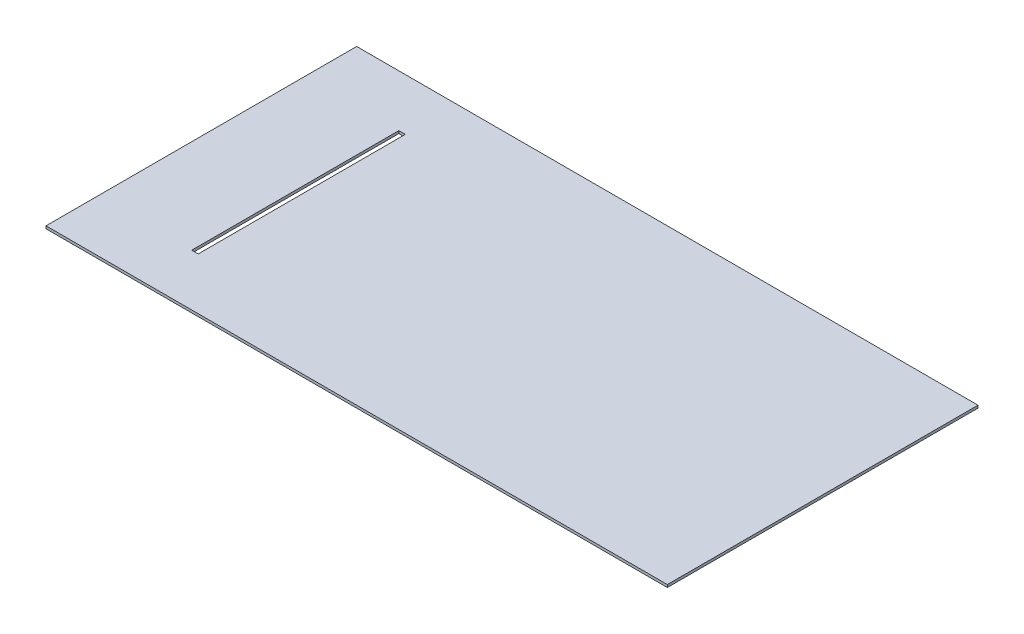
SolidWorks part; units mm, degrees
ref_plane "Front Plane" through (0, 0, 0) normal (0, 0, 1) x (1, 0, 0)
ref_plane "Top Plane" through (0, 0, 0) normal (0, 1, 0) x (1, 0, 0)
ref_plane "Right Plane" through (0, 0, 0) normal (1, 0, 0) x (0, 0, -1)
sketch "Sketch1" plane through (0, 0, 0) normal (0, 1, 0) x (1, 0, 0)
  line L1 (0, 0) -> (609.6, 0)
  line L2 (0, 0) -> (0, 304.8)
  line L3 (0, 304.8) -> (609.6, 304.8)
  line L4 (609.6, 0) -> (609.6, 304.8)
  dimension "D1" = 609.6
  dimension "D2" = 304.8
extrude "Boss-Extrude1" add sketch "Sketch1" along normal blind 2.54
sketch "Sketch2" plane through (0, 2.54, 0) normal (0, 1, 0) x (1, 0, 0)
  line L0 (609.6, 304.8) -> (0, 304.8) construction
  line L1 (92.2035, 254) -> (98.5535, 254)
  line L2 (92.2035, 254) -> (92.2035, 50.8)
  line L3 (92.2035, 50.8) -> (98.5535, 50.8)
  line L4 (98.5535, 254) -> (98.5535, 50.8)
  dimension "D1" = 203.2
  dimension "D2" = 50.8
  dimension "D3" = 6.35
extrude "Cut-Extrude1" cut sketch "Sketch2" against normal blind 54.864
